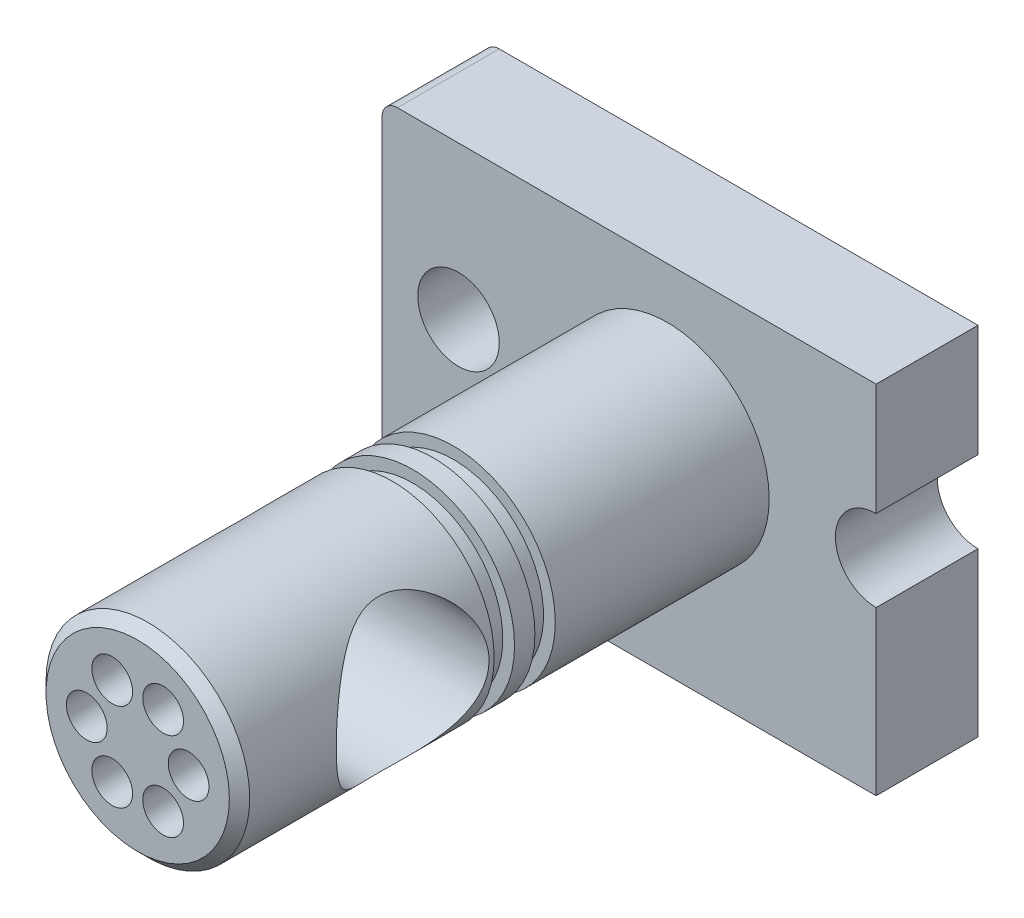
SolidWorks part; units mm, degrees
ref_plane "Front Plane" through (0, 0, 0) normal (0, 0, 1) x (1, 0, 0)
ref_plane "Top Plane" through (0, 0, 0) normal (0, 1, 0) x (1, 0, 0)
ref_plane "Right Plane" through (0, 0, 0) normal (1, 0, 0) x (0, 0, -1)
sketch "Sketch1" plane through (0, 0, 0) normal (0, 0, 1) x (1, 0, 0)
  line L0 (41, -8) -> (41, -40)
  line L1 (41, 30) -> (-56, 30)
  line L2 (41, 30) -> (41, 8)
  line L3 (41, -40) -> (-56, -40)
  line L4 (-56, 30) -> (-56, -40)
  circle A0 centre (-41, 0) radius 8
  arc A1 (41, 8) -> (41, -8) centre (41, 0) ccw
  point P9 (0, 0)
  dimension "D5" = 16
  dimension "D1" = 70
  dimension "D2" = 97
  dimension "D3" = 40
  dimension "D4" = 56
  dimension "D6" = 15
extrude "Boss-Extrude1" add sketch "Sketch1" along normal blind 20
sketch "Sketch2" plane through (0, 0, 20) normal (0, 0, 1) x (1, 0, 0)
  circle A0 centre (0, 0) radius 20
  dimension "D1" = 40
extrude "Boss-Extrude2" add sketch "Sketch2" along normal blind 104
sketch "Sketch3" plane through (0, 0, 0) normal (1, 0, 0) x (0, 0, -1)
  circle A0 centre (-90, 0) radius 15
  dimension "D1" = 30
  dimension "D2" = 90
extrude "Cut-Extrude1" cut sketch "Sketch3" against normal through all both and the other way through all
sketch "Sketch4" plane through (0, 0, 0) normal (1, 0, 0) x (0, 0, -1)
  line L0 (-20, 20) -> (-124, 20) construction
  line L1 (-74, 20) -> (-70, 20)
  line L2 (-74, 20) -> (-74, 17.7)
  line L3 (-74, 17.7) -> (-70, 17.7)
  line L4 (-70, 20) -> (-70, 17.7)
  line L5 (-20, 8) -> (-20, 30) construction
  line L6 (-66, 20) -> (-62, 20)
  line L7 (-66, 20) -> (-66, 17.7)
  line L8 (-66, 17.7) -> (-62, 17.7)
  line L9 (-62, 20) -> (-62, 17.7)
  line L10 (0, 0) -> (-133.7463, 0) construction
  dimension "D1" = 4
  dimension "D2" = 4
  dimension "D3" = 4
  dimension "D4" = 2.3
  dimension "D5" = 42
revolve "Cut-Revolve1" cut sketch "Sketch4" angle 360 about L10
sketch "Sketch5" plane through (0, 0, 124) normal (0, 0, 1) x (1, 0, 0)
  circle A0 centre (0, 0) radius 10 construction
  circle A1 centre (10, 0) radius 4
  dimension "D1" = 20
  dimension "D2" = 8
extrude "Cut-Extrude2" cut sketch "Sketch5" against normal blind 30
pattern_circular "CirPattern1" count 6 over 360 about axis through (0, 0, 0) along (0, 0, 1) of "Cut-Extrude2"
fillet "Fillet1" radius 3 2 edges at (-56, -40, 10) (-56, 30, 10)
chamfer "Chamfer1" distance 2 1 edges at (20, 0, 124)
